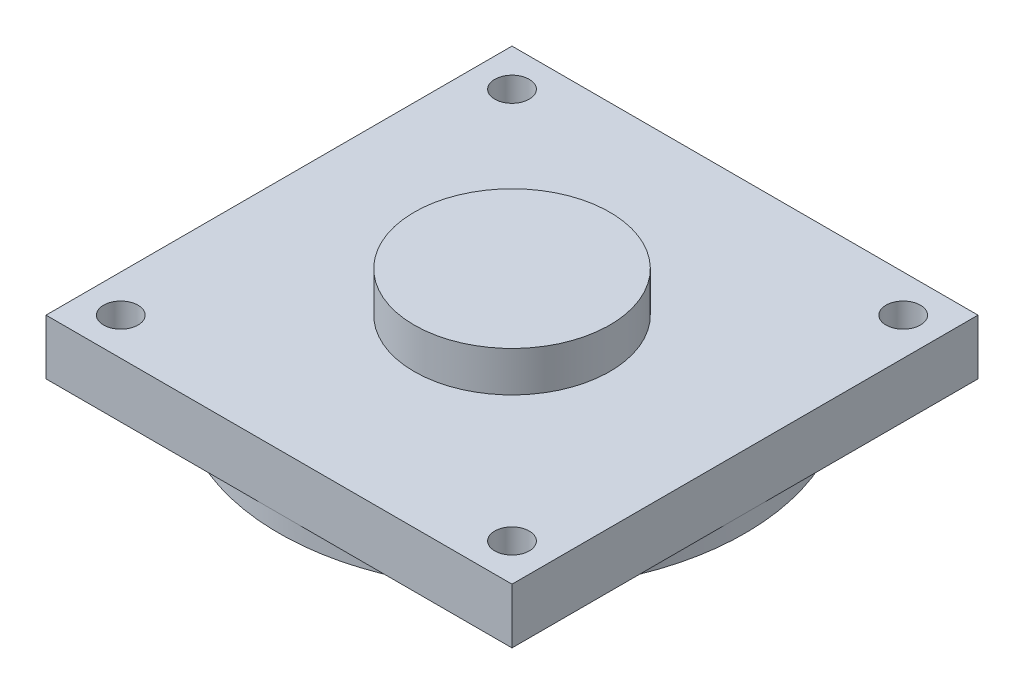
SolidWorks part; units mm, degrees
ref_plane "Front Plane" through (0, 0, 0) normal (0, 0, 1) x (1, 0, 0)
ref_plane "Top Plane" through (0, 0, 0) normal (0, 1, 0) x (1, 0, 0)
ref_plane "Right Plane" through (0, 0, 0) normal (1, 0, 0) x (0, 0, -1)
sketch "Sketch1" plane through (0, 0, 0) normal (0, 1, 0) x (1, 0, 0)
  line L1 (-20.25, 20.25) -> (20.25, 20.25)
  line L2 (-20.25, 20.25) -> (-20.25, -20.25)
  line L3 (-20.25, -20.25) -> (20.25, -20.25)
  line L4 (20.25, 20.25) -> (20.25, -20.25)
  point P0 (0, 0)
  dimension "D1" = 40.5
  dimension "D2" = 40.5
extrude "Boss-Extrude1" add sketch "Sketch1" along normal blind 4.8
sketch "Sketch2" plane through (0, 4.8, 0) normal (0, 1, 0) x (1, 0, 0)
  circle A0 centre (0, 0) radius 8.5
  dimension "D1" = 17
extrude "Boss-Extrude2" add sketch "Sketch2" along normal blind 3.5
sketch "Sketch3" plane through (0, 4.8, 0) normal (0, 1, 0) x (1, 0, 0)
  line L0 (-20.25, -20.25) -> (20.25, -20.25) construction
  line L1 (20.25, -20.25) -> (20.25, 20.25) construction
  line L2 (-20.25, 20.25) -> (-20.25, -20.25) construction
  line L3 (20.25, 20.25) -> (-20.25, 20.25) construction
  circle A0 centre (17, 17) radius 1.5
  circle A1 centre (-17, 17) radius 1.5
  circle A2 centre (-17, -17) radius 1.5
  circle A3 centre (17, -17) radius 1.5
  point P12 (-1.3411, -8.676)
  point P13 (0, 0)
  point P15 (-17.8774, -16.7376)
  dimension "D3" = 3
  dimension "D6" = 3
  dimension "D9" = 3
  dimension "D12" = 3
  dimension "D1" = 3.25
  dimension "D2" = 3.25
  dimension "D4" = 3.25
  dimension "D5" = 3.25
  dimension "D7" = 3.25
  dimension "D8" = 3.25
  dimension "D10" = 3.25
  dimension "D11" = 3.25
extrude "Cut-Extrude1" cut sketch "Sketch3" against normal blind 4.8
sketch "Sketch4" plane through (0, 0, 0) normal (0, -1, 0) x (-1, 0, 0)
  circle A0 centre (0, 0) radius 20.25
  dimension "D1" = 40.5
extrude "Boss-Extrude3" add sketch "Sketch4" along normal blind 1.5
